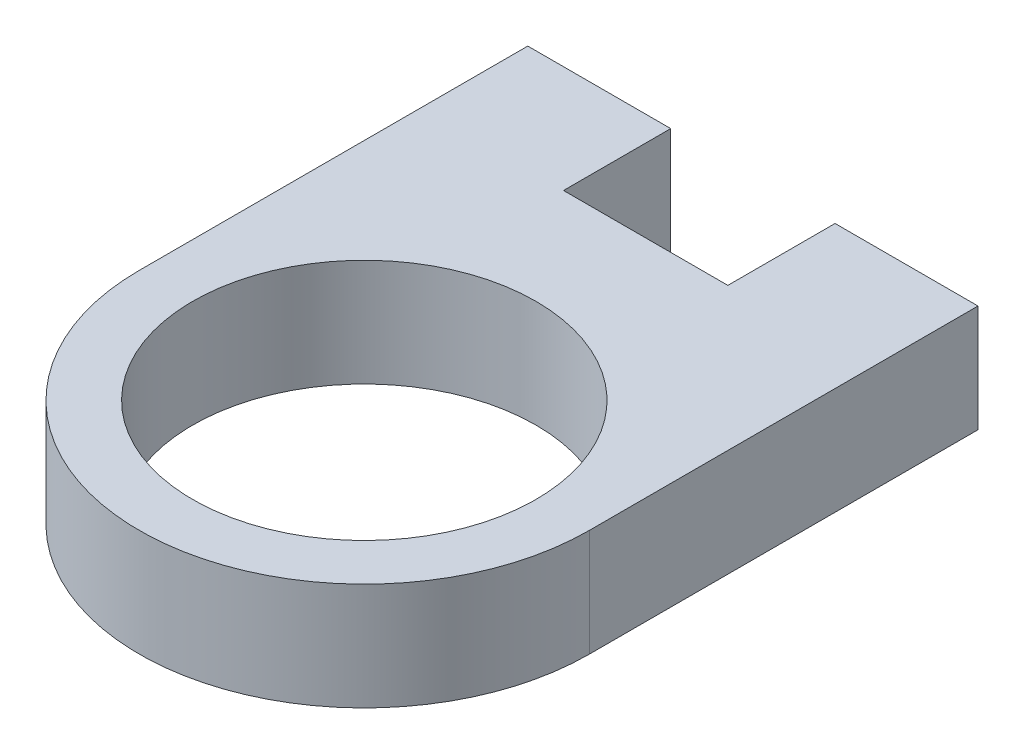
SolidWorks part; units mm, degrees
ref_plane "Front Plane" through (0, 0, 0) normal (0, 0, 1) x (1, 0, 0)
ref_plane "Top Plane" through (0, 0, 0) normal (0, 1, 0) x (1, 0, 0)
ref_plane "Right Plane" through (0, 0, 0) normal (1, 0, 0) x (0, 0, -1)
sketch "Sketch1" plane through (0, 0, 0) normal (0, 1, 0) x (1, 0, 0)
  line L1 (0, 0) -> (32, 0)
  line L2 (0, 0) -> (0, 20)
  line L3 (0, 20) -> (32, 20)
  line L4 (32, 0) -> (32, 20)
  arc A0 (0, 0) -> (32, 0) centre (16, 0) ccw
  dimension "D1" = 20
  dimension "D2" = 32
extrude "Boss-Extrude1" add sketch "Sketch1" along normal blind 7.62 contours L2 L3 L4 A0
sketch "Sketch2" plane through (0, 0, 0) normal (0, -1, 0) x (1, 0, 0)
  line L0 (32, 0) -> (0, 0) construction
  circle A0 centre (16, 0) radius 12.2
extrude "Cut-Extrude1" cut sketch "Sketch2" against normal through all
sketch "Sketch3" plane through (0, 0, -20) normal (0, 0, -1) x (-1, 0, 0)
  line L0 (0, 0) -> (-32, 0) construction
  line L1 (-32, 7.62) -> (-21.84, 7.62)
  line L2 (-32, 7.62) -> (-32, 0)
  line L3 (-32, 0) -> (-21.84, 0)
  line L4 (-21.84, 7.62) -> (-21.84, 0)
  line L6 (0, 7.62) -> (-10.16, 7.62)
  line L7 (0, 7.62) -> (0, 0)
  line L8 (0, 0) -> (-10.16, 0)
  line L9 (-10.16, 7.62) -> (-10.16, 0)
  dimension "D1" = 10.16
  dimension "D2" = 10.16
  dimension "D3" = 11.68
extrude "Boss-Extrude2" add sketch "Sketch3" along normal blind 7.62
equation "\"MDF\" = 0.3in"
equation "\"D1@Boss-Extrude1\"=\"MDF\""
equation "\"D1@Boss-Extrude2\"=\"MDF\""
